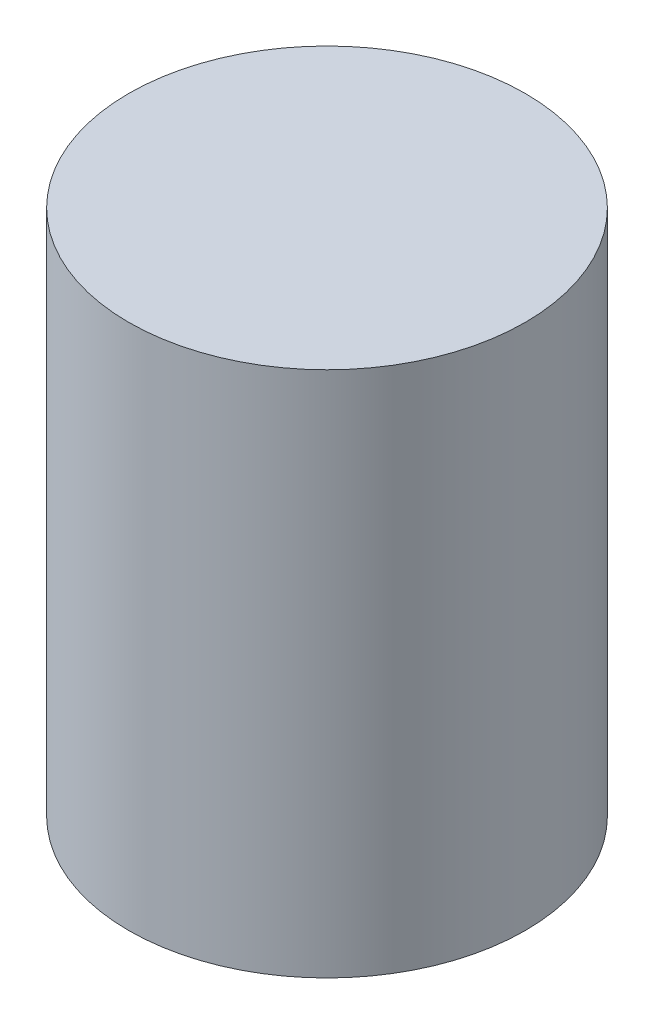
SolidWorks part; units mm, degrees
ref_plane "Front Plane" through (0, 0, 0) normal (0, 0, 1) x (1, 0, 0)
ref_plane "Top Plane" through (0, 0, 0) normal (0, 1, 0) x (1, 0, 0)
ref_plane "Right Plane" through (0, 0, 0) normal (1, 0, 0) x (0, 0, -1)
sketch "Sketch1" plane through (0, 0, 0) normal (0, 1, 0) x (1, 0, 0)
  circle A0 centre (0, 0) radius 99
  dimension "D1" = 198
extrude "Boss-Extrude1" add sketch "Sketch1" along normal mid plane 263
